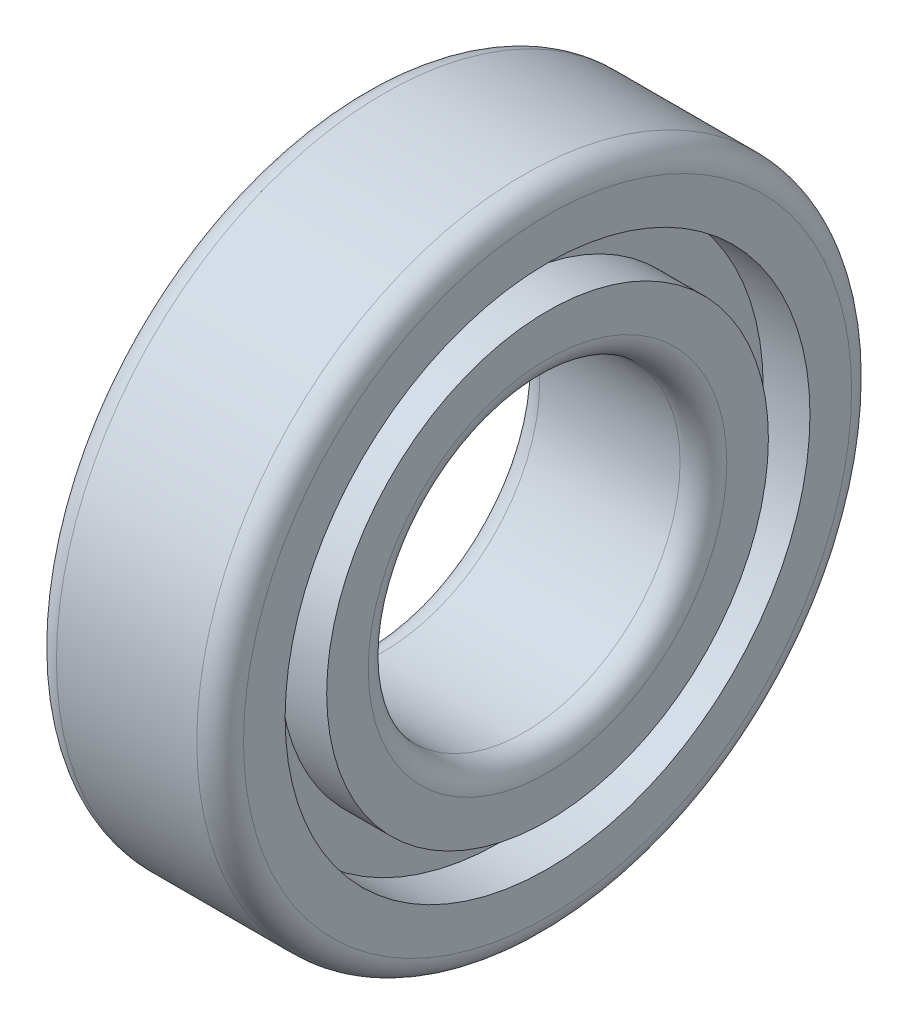
SolidWorks part; units mm, degrees
material "AISI 1020"
ref_plane "Спереди" through (0, 0, 0) normal (0, 0, 1) x (1, 0, 0)
ref_plane "Сверху" through (0, 0, 0) normal (0, 1, 0) x (1, 0, 0)
ref_plane "Справа" through (0, 0, 0) normal (1, 0, 0) x (0, 0, -1)
sketch "Эскиз1" plane through (0, 0, 0) normal (0, 0, 1) x (1, 0, 0)
  line L0 (4.5, 10) -> (-4.5, 10)
  line L1 (-6, 11.5) -> (-6, 14.1667)
  line L2 (-6, 14.1667) -> (-3, 14.1667)
  line L3 (-3, 14.1667) -> (-3, 16.8333)
  line L4 (-3, 16.8333) -> (-6, 16.8333)
  line L5 (-6, 16.8333) -> (-6, 19.5)
  line L6 (-4.5, 21) -> (4.5, 21)
  line L7 (-873.9917, 0) -> (42825.5954, 0) construction
  line L8 (0, -873.9917) -> (0, 42825.5954) construction
  line L9 (6, 16.8333) -> (6, 19.5)
  line L10 (3, 16.8333) -> (6, 16.8333)
  line L11 (3, 14.1667) -> (3, 16.8333)
  line L12 (6, 14.1667) -> (3, 14.1667)
  line L13 (6, 11.5) -> (6, 14.1667)
  arc A0 (-4.5, 10) -> (-6, 11.5) centre (-4.5, 11.5) cw
  arc A1 (-6, 19.5) -> (-4.5, 21) centre (-4.5, 19.5) cw
  arc A2 (6, 19.5) -> (4.5, 21) centre (4.5, 19.5) ccw
  arc A3 (4.5, 10) -> (6, 11.5) centre (4.5, 11.5) ccw
  point P25 (0, 21)
  point P29 (0, 10)
  dimension "D3" = 1.5
  dimension "B" = 12
  dimension "D1" = 20
  dimension "D2" = 42
  dimension "D4" = 3
revolve "Повернуть1" add sketch "Эскиз1" angle 360 about L7
equation "\"D4@Эскиз1\"=\"B@Эскиз1\"/4"
